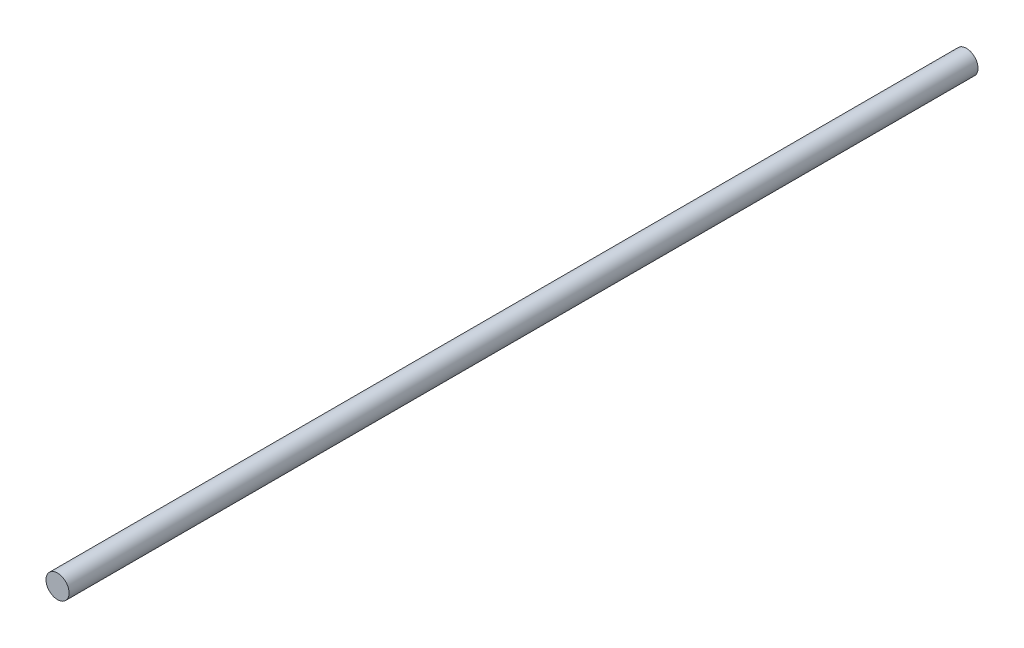
SolidWorks part; units mm, degrees
ref_plane "前视基准面" through (0, 0, 0) normal (0, 0, 1) x (1, 0, 0)
ref_plane "上视基准面" through (0, 0, 0) normal (0, 1, 0) x (1, 0, 0)
ref_plane "右视基准面" through (0, 0, 0) normal (1, 0, 0) x (0, 0, -1)
other "Configuration Table"
sketch "Sketch1" plane through (0, 0, 0) normal (0, 0, 1) x (1, 0, 0)
  circle A0 centre (0, 0) radius 4
  dimension "D1" = 8
extrude "Boss-Extrude1" add sketch "Sketch1" along normal blind 315
